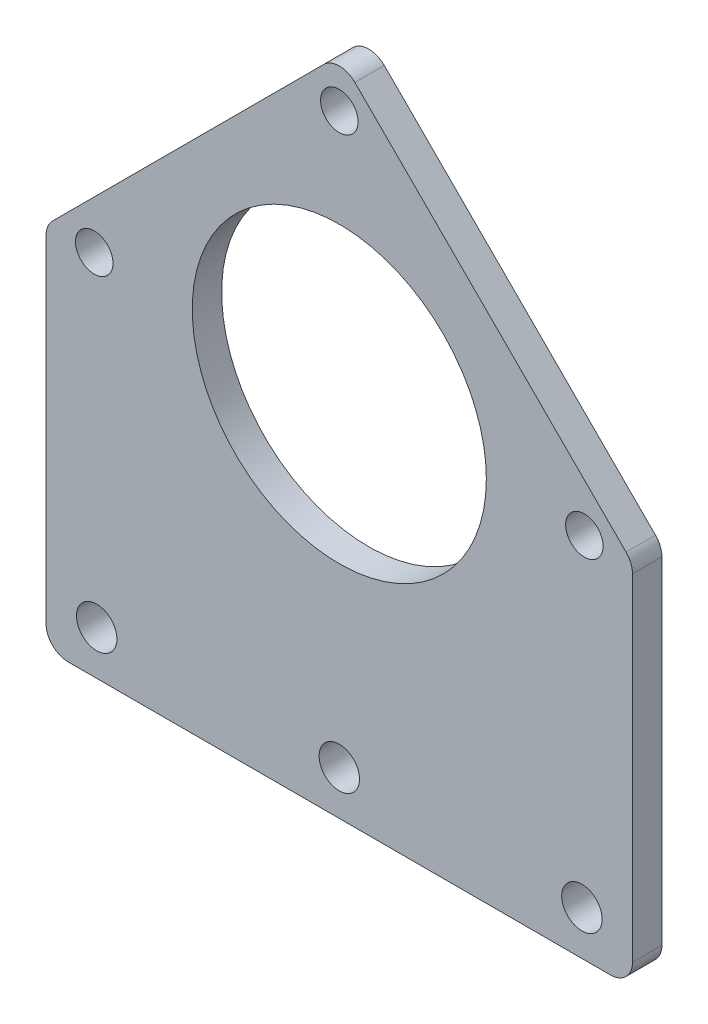
SolidWorks part; units mm, degrees
ref_plane "Спереди" through (0, 0, 0) normal (0, 0, 1) x (1, 0, 0)
ref_plane "Сверху" through (0, 0, 0) normal (0, 1, 0) x (1, 0, 0)
ref_plane "Справа" through (0, 0, 0) normal (1, 0, 0) x (0, 0, -1)
sketch "Эскиз1" plane through (0, 0, 0) normal (0, 0, 1) x (1, 0, 0)
  line L0 (-39.8808, 0) -> (0, 39.8808)
  line L1 (-39.8808, 0) -> (-39.8808, -50)
  line L2 (-39.8808, -50) -> (39.8808, -50)
  line L11 (39.8808, -50) -> (39.8808, 0)
  line L12 (0, 39.8808) -> (39.8808, 0)
  circle A0 centre (0, 0) radius 20
  circle A1 centre (-33.333, 0) radius 2.55
  circle A2 centre (0, 33.333) radius 2.55
  circle A3 centre (33.333, 0) radius 2.55
  circle A4 centre (-33, -44) radius 2.75
  circle A5 centre (0, -44) radius 2.75
  circle A6 centre (33, -44) radius 2.75
  point P4 (0, 0)
  point P23 (0, 0)
  point P27 (0, 0)
  dimension "D2" = 40
  dimension "D4" = 5.1
  dimension "D6" = 56.4
  dimension "D5" = 47.14
  dimension "D7" = 90
  dimension "D8" = 33
  dimension "D9" = 50
  dimension "D1" = 6
  dimension "D10" = 33
  dimension "D11" = 5.5
  dimension "D3" = 3
extrude "Бобышка-Вытянуть2" add sketch "Эскиз1" along normal blind 4
fillet "Скругление1" radius 3 5 edges at (39.8808, 0, 2) (-39.8808, 0, 2) (0, 39.8808, 2) (-39.8808, -50, 2) (39.8808, -50, 2)
